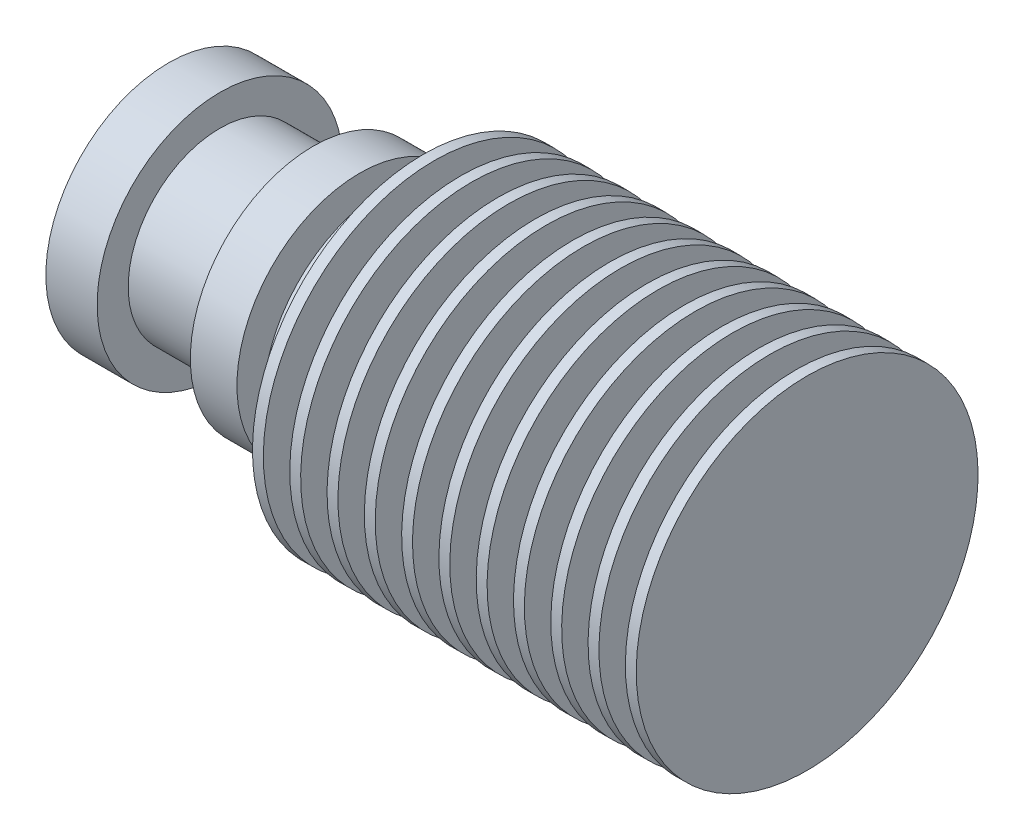
SolidWorks part; units mm, degrees
material "7075-T6 (SN)"
ref_plane "Plano frontal" through (0, 0, 0) normal (0, 0, 1) x (1, 0, 0)
ref_plane "Plano superior" through (0, 0, 0) normal (0, 1, 0) x (1, 0, 0)
ref_plane "Plano direito" through (0, 0, 0) normal (1, 0, 0) x (0, 0, -1)
sketch "Esboço1" plane through (0, 0, 0) normal (0, 0, 1) x (1, 0, 0)
  line L0 (-23.5, 7.9) -> (-23.5, 2.1) construction
  line L1 (-23.5, 5) -> (-69.1, 5) construction
  line L2 (-28, 5) -> (-28, 16)
  line L3 (-28, 16) -> (-28.7, 16)
  line L4 (-28.7, 16) -> (-28.7, 10)
  line L5 (-28.7, 10) -> (-30.4, 10)
  line L7 (-30.4, 10) -> (-30.4, 16)
  line L8 (-30.4, 16) -> (-31.1, 16)
  line L9 (-31.1, 16) -> (-31.1, 10)
  line L10 (-31.1, 10) -> (-32.8, 10)
  line L11 (-32.8, 10) -> (-32.8, 16)
  line L12 (-32.8, 16) -> (-33.5, 16)
  line L13 (-33.5, 16) -> (-33.5, 10)
  line L14 (-33.5, 10) -> (-35.2, 10)
  line L15 (-35.2, 10) -> (-35.2, 16)
  line L16 (-35.2, 16) -> (-35.9, 16)
  line L17 (-35.9, 16) -> (-35.9, 10)
  line L18 (-35.9, 10) -> (-37.6, 10)
  line L19 (-37.6, 10) -> (-37.6, 16)
  line L20 (-37.6, 16) -> (-38.3, 16)
  line L21 (-38.3, 16) -> (-38.3, 10)
  line L22 (-38.3, 10) -> (-40, 10)
  line L23 (-40, 10) -> (-40, 16)
  line L24 (-40, 16) -> (-40.7, 16)
  line L25 (-40.7, 16) -> (-40.7, 10)
  line L26 (-40.7, 10) -> (-42.4, 10)
  line L27 (-42.4, 10) -> (-42.4, 16)
  line L28 (-42.4, 16) -> (-43.1, 16)
  line L29 (-43.1, 16) -> (-43.1, 10)
  line L30 (-43.1, 10) -> (-44.8, 10)
  line L31 (-44.8, 10) -> (-44.8, 16)
  line L32 (-44.8, 16) -> (-45.5, 16)
  line L33 (-45.5, 16) -> (-45.5, 10)
  line L34 (-45.5, 10) -> (-47.2, 10)
  line L35 (-47.2, 10) -> (-47.2, 16)
  line L36 (-47.2, 16) -> (-47.9, 16)
  line L37 (-47.9, 16) -> (-47.9, 10)
  line L38 (-47.9, 10) -> (-49.6, 10)
  line L39 (-49.6, 10) -> (-49.6, 16)
  line L40 (-49.6, 16) -> (-50.3, 16)
  line L41 (-50.3, 16) -> (-50.3, 10)
  line L42 (-50.3, 10) -> (-52, 10)
  line L43 (-52, 10) -> (-52, 16)
  line L44 (-52, 16) -> (-52.7, 16)
  line L45 (-52.7, 16) -> (-52.7, 10)
  line L46 (-52.7, 10) -> (-54.4, 10)
  line L47 (-54.4, 10) -> (-54.4, 12.9)
  line L48 (-54.4, 12.9) -> (-55.1, 12.9)
  line L49 (-55.1, 12.9) -> (-55.1, 10)
  line L50 (-55.1, 10) -> (-56.8, 10)
  line L51 (-56.8, 10) -> (-56.8, 12.9)
  line L52 (-56.8, 12.9) -> (-59.8, 12.9)
  line L53 (-59.8, 12.9) -> (-59.8, 10.9)
  line L54 (-59.8, 10.9) -> (-65.8, 10.9)
  line L55 (-65.8, 10.9) -> (-65.8, 12.9)
  line L56 (-65.8, 12.9) -> (-69.1, 12.9)
  line L57 (-69.1, 12.9) -> (-69.1, 5)
  line L58 (-28, 5) -> (-69.1, 5)
  dimension "D1" = 11
  dimension "D2" = 0.7
  dimension "D3" = 1.7
  dimension "D5" = 5
  dimension "D7" = 7.9
  dimension "D8" = 3
  dimension "D9" = 6
  dimension "D10" = 3.3
  dimension "D11" = 5.9
  dimension "D6" = 11
revolve "Revolução1" add sketch "Esboço1" angle 360 about L58
sketch "Sketch1" plane through (-69.1, 0, 0) normal (-1, 0, 0) x (0, 0, 1)
  circle A0 centre (0, 5) radius 3.5
  circle A1 centre (0, 5) radius 7.9 construction
  dimension "D1" = 7
extrude "Cut-Extrude1" cut sketch "Sketch1" against normal blind 10
